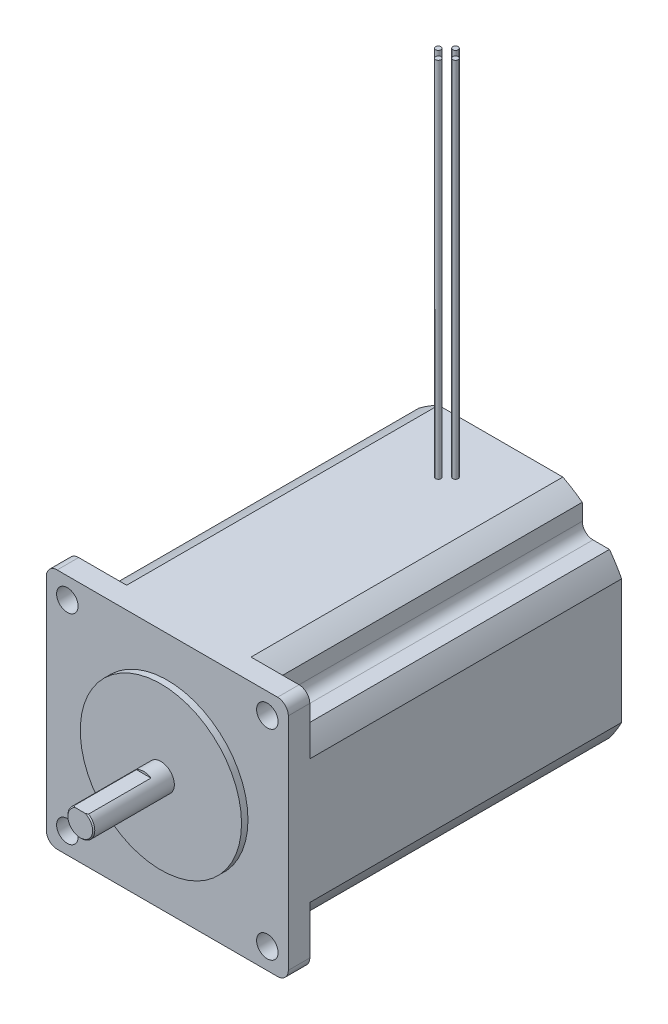
SolidWorks part; units mm, degrees
material "Plain Carbon Steel"
ref_plane "Front Plane" through (0, 0, 0) normal (0, 0, 1) x (1, 0, 0)
ref_plane "Top Plane" through (0, 0, 0) normal (0, 1, 0) x (1, 0, 0)
ref_plane "Right Plane" through (0, 0, 0) normal (1, 0, 0) x (0, 0, -1)
ref_plane "Plane1" through (0, -28.575, 0) normal (0, -1, 0) x (1, 0, 0)
sketch "Sketch1" plane through (0, -28.575, 0) normal (0, -1, 0) x (1, 0, 0)
  line L0 (-28.575, 0) -> (28.575, 0)
  line L1 (28.575, 0) -> (28.575, 78.74)
  line L2 (28.575, 78.74) -> (-28.575, 78.74)
  line L3 (-28.575, 78.74) -> (-28.575, 0)
extrude "Boss-Extrude1" add sketch "Sketch1" against normal blind 57.15
sketch "Sketch2" plane through (0, 0, 0) normal (0, 0, -1) x (-1, 0, 0)
  line L0 (-28.575, -28.575) -> (-14.6925, -28.575)
  line L1 (-28.575, -14.6925) -> (-28.575, -28.575)
  arc A0 (-14.6925, -28.575) -> (-28.575, -14.6925) centre (0, 0) cw
extrude "Cut-Extrude1" cut sketch "Sketch2" against normal blind 73.66
sketch "Sketch3" plane through (0, 0, 0) normal (0, 0, -1) x (-1, 0, 0)
  line L0 (-19.2786, -25.7048) -> (-19.2786, -19.2786)
  line L1 (-19.2786, -19.2786) -> (-25.7048, -19.2786)
  arc A0 (-25.7048, -19.2786) -> (-19.2786, -25.7048) centre (0, 0) ccw
extrude "Cut-Extrude2" cut sketch "Sketch3" against normal blind 73.66
sketch "Sketch4" plane through (0, 0, 0) normal (0, 0, -1) x (-1, 0, 0)
  line L0 (-28.575, 28.575) -> (-28.575, 14.6925)
  line L1 (-14.6925, 28.575) -> (-28.575, 28.575)
  arc A0 (-28.575, 14.6925) -> (-14.6925, 28.575) centre (0, 0) cw
extrude "Cut-Extrude3" cut sketch "Sketch4" against normal blind 73.66
sketch "Sketch5" plane through (0, 0, 0) normal (0, 0, -1) x (-1, 0, 0)
  line L0 (-25.7048, 19.2786) -> (-19.2786, 19.2786)
  line L1 (-19.2786, 19.2786) -> (-19.2786, 25.7048)
  arc A0 (-19.2786, 25.7048) -> (-25.7048, 19.2786) centre (0, 0) ccw
extrude "Cut-Extrude4" cut sketch "Sketch5" against normal blind 73.66
sketch "Sketch6" plane through (0, 0, 0) normal (0, 0, -1) x (-1, 0, 0)
  line L0 (28.575, 28.575) -> (14.6925, 28.575)
  line L1 (28.575, 14.6925) -> (28.575, 28.575)
  arc A0 (14.6925, 28.575) -> (28.575, 14.6925) centre (0, 0) cw
extrude "Cut-Extrude5" cut sketch "Sketch6" against normal blind 73.66
sketch "Sketch7" plane through (0, 0, 0) normal (0, 0, -1) x (-1, 0, 0)
  line L0 (19.2786, 25.7048) -> (19.2786, 19.2786)
  line L1 (19.2786, 19.2786) -> (25.7048, 19.2786)
  arc A0 (25.7048, 19.2786) -> (19.2786, 25.7048) centre (0, 0) ccw
extrude "Cut-Extrude6" cut sketch "Sketch7" against normal blind 73.66
sketch "Sketch8" plane through (0, 0, 0) normal (0, 0, -1) x (-1, 0, 0)
  line L0 (28.575, -28.575) -> (28.575, -14.6925)
  line L1 (14.6925, -28.575) -> (28.575, -28.575)
  arc A0 (28.575, -14.6925) -> (14.6925, -28.575) centre (0, 0) cw
extrude "Cut-Extrude7" cut sketch "Sketch8" against normal blind 73.66
sketch "Sketch9" plane through (0, 0, 0) normal (0, 0, -1) x (-1, 0, 0)
  line L0 (25.7048, -19.2786) -> (19.2786, -19.2786)
  line L1 (19.2786, -19.2786) -> (19.2786, -25.7048)
  arc A0 (19.2786, -25.7048) -> (25.7048, -19.2786) centre (0, 0) ccw
extrude "Cut-Extrude8" cut sketch "Sketch9" against normal blind 73.66
sketch "Sketch10" plane through (0, 0, 78.74) normal (0, 0, 1) x (1, 0, 0)
  circle A0 centre (0, 0) radius 19.05
extrude "Boss-Extrude2" add sketch "Sketch10" along normal blind 1.524
sketch "Sketch11" plane through (0, 0, 80.264) normal (0, 0, 1) x (1, 0, 0)
  circle A0 centre (0, 0) radius 3.175
extrude "Boss-Extrude3" add sketch "Sketch11" along normal blind 19.05
sketch "Sketch12" plane through (0, 0, 99.314) normal (0, 0, 1) x (1, 0, 0)
  line L0 (-1.7227, 2.667) -> (1.7227, 2.667)
  arc A0 (1.7227, 2.667) -> (-1.7227, 2.667) centre (0, 0) ccw
extrude "Cut-Extrude9" cut sketch "Sketch12" against normal blind 14.986
ref_plane "Plane2" through (0, 0, 12.7) normal (0, 0, -1) x (-1, 0, 0)
sketch "Sketch13" plane through (0, 0, 12.7) normal (0, 0, -1) x (-1, 0, 0)
  line L0 (1.397, 28.575) -> (2.032, 28.575)
  line L1 (2.032, 28.575) -> (2.032, 114.3)
  line L2 (2.032, 114.3) -> (1.397, 114.3)
  line L3 (1.397, 114.3) -> (1.397, 28.575)
  line L4 (2.032, 28.575) -> (2.032, 114.3) construction
revolve "Revolve1" add sketch "Sketch13" angle 360 about L4
sketch "Sketch14" plane through (0, 0, 12.7) normal (0, 0, -1) x (-1, 0, 0)
  line L0 (-2.667, 28.575) -> (-2.032, 28.575)
  line L1 (-2.032, 28.575) -> (-2.032, 114.3)
  line L2 (-2.032, 114.3) -> (-2.667, 114.3)
  line L3 (-2.667, 114.3) -> (-2.667, 28.575)
  line L4 (-2.032, 28.575) -> (-2.032, 114.3) construction
revolve "Revolve2" add sketch "Sketch14" angle 360 about L4
ref_plane "Plane3" through (0, 0, 14.732) normal (0, 0, -1) x (-1, 0, 0)
sketch "Sketch15" plane through (0, 0, 14.732) normal (0, 0, -1) x (-1, 0, 0)
  line L0 (-0.635, 28.575) -> (0, 28.575)
  line L1 (0, 28.575) -> (0, 114.3)
  line L2 (0, 114.3) -> (-0.635, 114.3)
  line L3 (-0.635, 114.3) -> (-0.635, 28.575)
  line L4 (0, 28.575) -> (0, 114.3) construction
revolve "Revolve3" add sketch "Sketch15" angle 360 about L4
ref_plane "Plane4" through (0, 0, 10.668) normal (0, 0, -1) x (-1, 0, 0)
sketch "Sketch16" plane through (0, 0, 10.668) normal (0, 0, -1) x (-1, 0, 0)
  line L0 (-0.635, 28.575) -> (0, 28.575)
  line L1 (0, 28.575) -> (0, 114.3)
  line L2 (0, 114.3) -> (-0.635, 114.3)
  line L3 (-0.635, 114.3) -> (-0.635, 28.575)
  line L4 (0, 28.575) -> (0, 114.3) construction
revolve "Revolve4" add sketch "Sketch16" angle 360 about L4
hole_wizard "Hole1" positions "Sketch18" profile "Sketch17" legacy
sketch "Sketch18" plane through (0, 0, 73.66) normal (0, 0, -1) x (-1, 0, 0)
  point P0 (23.622, -23.622)
sketch "Sketch17" plane through (-23.622, -23.622, 73.66) normal (1, 0, 0) x (0, 1, 0)
  line L0 (0, 0) -> (0, 25.654)
  line L1 (0, 25.654) -> (2.54, 25.654)
  line L2 (2.54, 25.654) -> (2.54, 0)
  line L3 (2.54, 0) -> (0, 0)
  line L4 (0, 110) -> (0, -10) construction
  dimension "Diameter" = 5.08
  dimension "Depth" = 25.654
hole_wizard "Hole2" positions "Sketch20" profile "Sketch19" legacy
sketch "Sketch20" plane through (0, 0, 73.66) normal (0, 0, -1) x (-1, 0, 0)
  point P0 (23.622, 23.622)
sketch "Sketch19" plane through (-23.622, 23.622, 73.66) normal (1, 0, 0) x (0, 1, 0)
  line L0 (0, 0) -> (0, 25.654)
  line L1 (0, 25.654) -> (2.54, 25.654)
  line L2 (2.54, 25.654) -> (2.54, 0)
  line L3 (2.54, 0) -> (0, 0)
  line L4 (0, 110) -> (0, -10) construction
  dimension "Diameter" = 5.08
  dimension "Depth" = 25.654
hole_wizard "Hole3" positions "Sketch22" profile "Sketch21" legacy
sketch "Sketch22" plane through (0, 0, 73.66) normal (0, 0, -1) x (-1, 0, 0)
  point P0 (-23.622, 23.622)
sketch "Sketch21" plane through (23.622, 23.622, 73.66) normal (1, 0, 0) x (0, 1, 0)
  line L0 (0, 0) -> (0, 25.654)
  line L1 (0, 25.654) -> (2.54, 25.654)
  line L2 (2.54, 25.654) -> (2.54, 0)
  line L3 (2.54, 0) -> (0, 0)
  line L4 (0, 110) -> (0, -10) construction
  dimension "Diameter" = 5.08
  dimension "Depth" = 25.654
hole_wizard "Hole4" positions "Sketch24" profile "Sketch23" legacy
sketch "Sketch24" plane through (0, 0, 73.66) normal (0, 0, -1) x (-1, 0, 0)
  point P0 (-23.622, -23.622)
sketch "Sketch23" plane through (23.622, -23.622, 73.66) normal (1, 0, 0) x (0, 1, 0)
  line L0 (0, 0) -> (0, 25.654)
  line L1 (0, 25.654) -> (2.54, 25.654)
  line L2 (2.54, 25.654) -> (2.54, 0)
  line L3 (2.54, 0) -> (0, 0)
  line L4 (0, 110) -> (0, -10) construction
  dimension "Diameter" = 5.08
  dimension "Depth" = 25.654
chamfer "Chamfer1" distance 0.254 angle 45 1 edges at (0, -3.175, 99.314)
fillet "Fillet1" radius 2.54 1 edges at (-28.575, 28.575, 76.2)
fillet "Fillet2" radius 2.54 1 edges at (-28.575, -28.575, 76.2)
fillet "Fillet3" radius 2.54 1 edges at (28.575, 28.575, 76.2)
fillet "Fillet4" radius 2.54 1 edges at (-19.2786, 19.2786, 36.83)
fillet "Fillet5" radius 2.54 1 edges at (28.575, -28.575, 76.2)
fillet "Fillet6" radius 2.54 1 edges at (19.2786, -19.2786, 36.83)
fillet "Fillet7" radius 2.54 1 edges at (19.2786, 19.2786, 36.83)
fillet "Fillet8" radius 2.54 1 edges at (-19.2786, -19.2786, 36.83)
